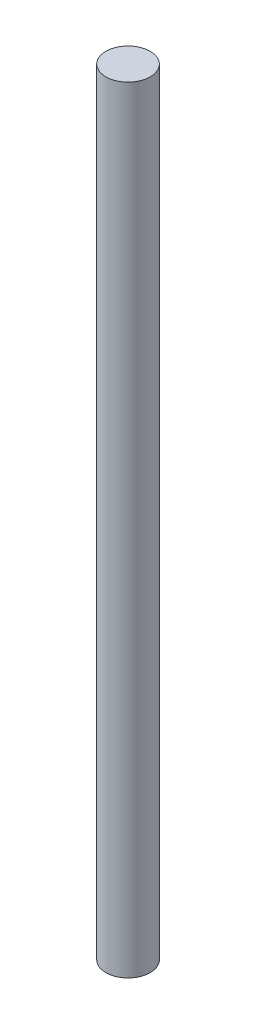
SolidWorks part; units mm, degrees
material "6061 Alloy"
ref_plane "Front Plane" through (0, 0, 0) normal (0, 0, 1) x (1, 0, 0)
ref_plane "Top Plane" through (0, 0, 0) normal (0, 1, 0) x (1, 0, 0)
ref_plane "Right Plane" through (0, 0, 0) normal (1, 0, 0) x (0, 0, -1)
sketch "Sketch1" plane through (0, 0, 0) normal (0, 0, 1) x (1, 0, 0)
  line L0 (0, 0) -> (0, 25.5113) construction
  line L1 (0, -35) -> (2, -35)
  line L2 (0, -35) -> (0, 35)
  line L3 (0, 35) -> (2, 35)
  line L4 (2, -35) -> (2, 35)
  dimension "D1" = 4
  dimension "D2" = 70
revolve "Revolve1" add sketch "Sketch1" angle 360 about L0
